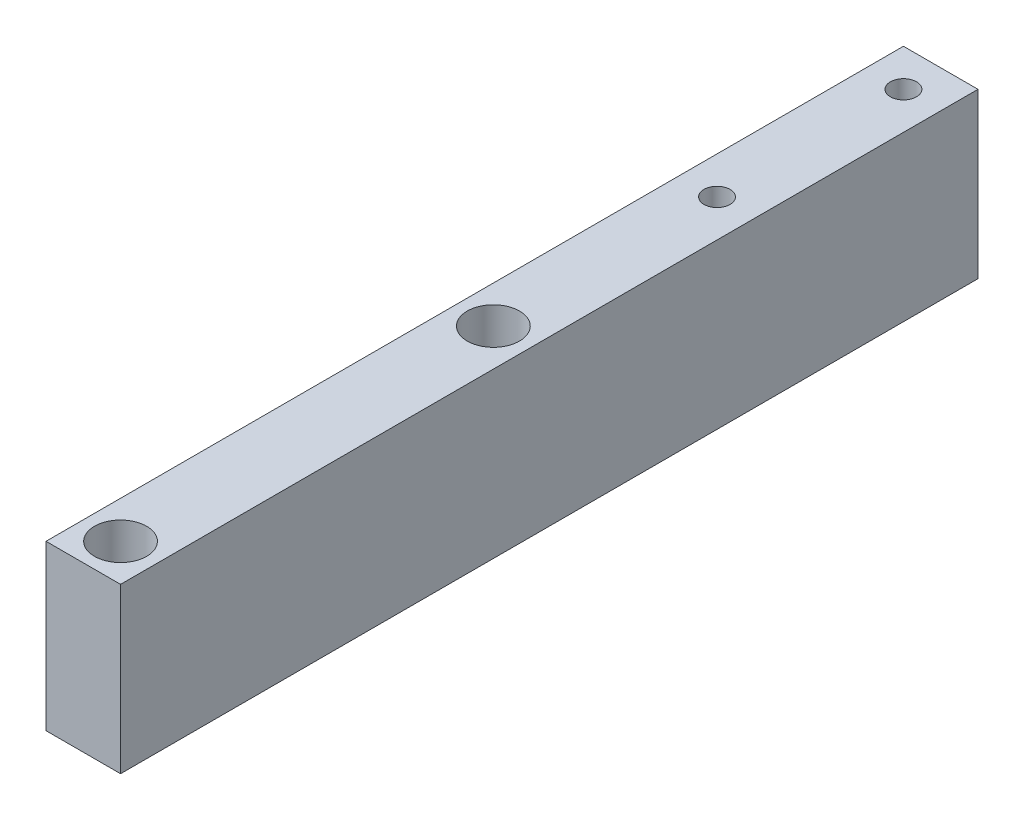
SolidWorks part; units mm, degrees
ref_plane "Front Plane" through (0, 0, 0) normal (0, 0, 1) x (1, 0, 0)
ref_plane "Top Plane" through (0, 0, 0) normal (0, 1, 0) x (1, 0, 0)
ref_plane "Right Plane" through (0, 0, 0) normal (1, 0, 0) x (0, 0, -1)
sketch "Sketch1" plane through (0, 0, 0) normal (0, 1, 0) x (1, 0, 0)
  line L1 (-5, 57.5) -> (5, 57.5)
  line L2 (-5, 57.5) -> (-5, -57.5)
  line L3 (-5, -57.5) -> (5, -57.5)
  line L4 (5, 57.5) -> (5, -57.5)
  line L5 (-5, 57.5) -> (5, -57.5) construction
  line L6 (-5, -57.5) -> (5, 57.5) construction
  point P0 (0, 0)
  dimension "D1" = 10
  dimension "D2" = 115
extrude "Boss-Extrude1" add sketch "Sketch1" along normal blind 22
sketch "Sketch3" plane through (0, 22, 0) normal (0, 1, 0) x (1, 0, 0)
  line L0 (0, -12.1) -> (0, 12.1) construction
  line L1 (-5, -57.5) -> (5, -57.5) construction
  circle A0 centre (0, -52.5) radius 2.05
  circle A1 centre (0, -2.5) radius 2.05
  dimension "D1" = 4.1
  dimension "D3" = 4.1
  dimension "D2" = 5
  dimension "D4" = 50
extrude "Cut-Extrude1" cut sketch "Sketch3" against normal up to surface (22 mm away) up to face at (0, 0, 0)
sketch "Sketch4" plane through (0, 22, 0) normal (0, 1, 0) x (1, 0, 0)
  circle A0 centre (0, -52.5) radius 3.5
  circle A1 centre (0, -2.5) radius 3.5
  dimension "D1" = 7
  dimension "D2" = 7
extrude "Cut-Extrude2" cut sketch "Sketch4" against normal offset from surface (12 mm away) 10 up to face at (0, 0, 54.55)
sketch "Sketch7" plane through (0, 22, 0) normal (0, 1, 0) x (1, 0, 0)
  line L0 (0, -12.1) -> (0, 12.1) construction
  line L1 (5, 57.5) -> (-5, 57.5) construction
  circle A0 centre (0, 52.5) radius 1.75
  circle A1 centre (0, 27.5) radius 1.75
  dimension "D1" = 3.5
  dimension "D3" = 3.5
  dimension "D2" = 5
  dimension "D4" = 25
extrude "Cut-Extrude3" cut sketch "Sketch7" against normal through all
